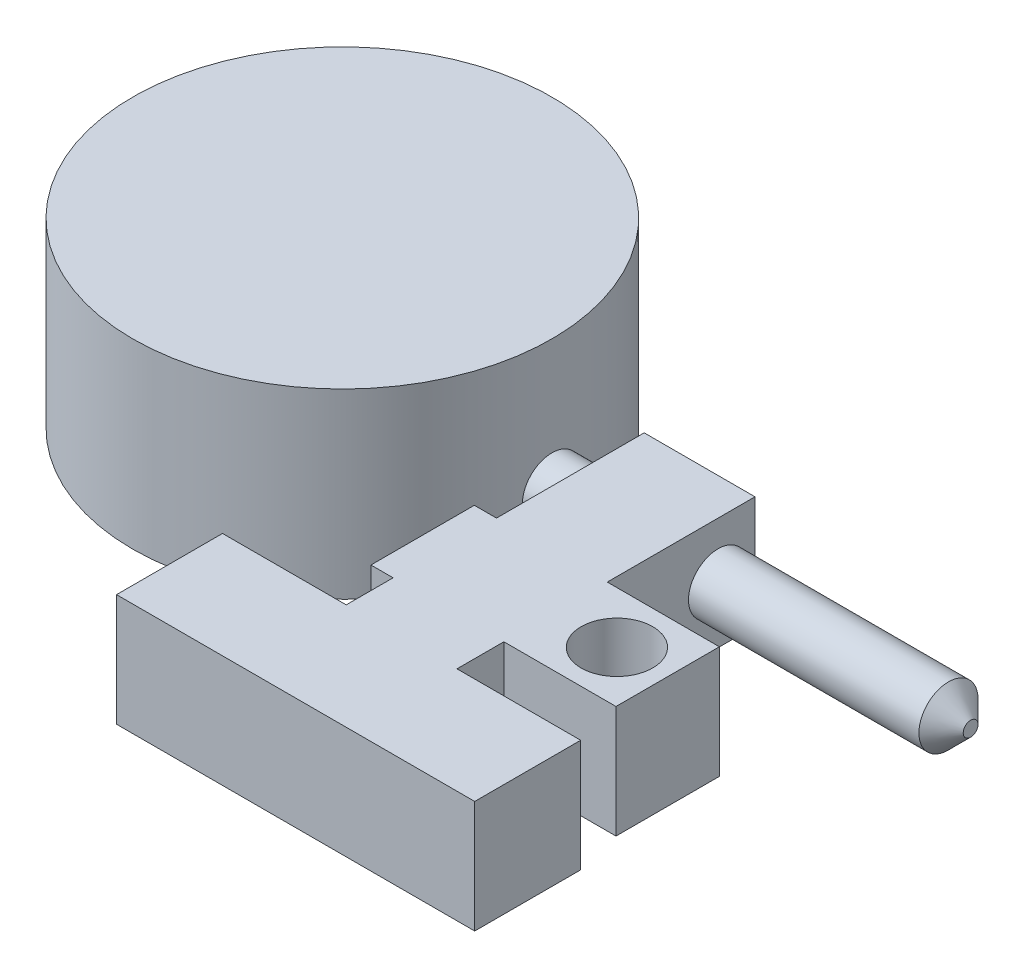
SolidWorks part; units mm, degrees
ref_plane "Front Plane" through (0, 0, 0) normal (0, 0, 1) x (1, 0, 0)
ref_plane "Top Plane" through (0, 0, 0) normal (0, 1, 0) x (1, 0, 0)
ref_plane "Right Plane" through (0, 0, 0) normal (1, 0, 0) x (0, 0, -1)
sketch "Sketch1" plane through (0, 0, 0) normal (0, 1, 0) x (1, 0, 0)
  circle A0 centre (0, 0) radius 28.375
  dimension "D1" = 56.75
extrude "Boss-Extrude1" add sketch "Sketch1" along normal blind 24.66
ref_plane "Plane1" through (28.375, 0, 0) normal (1, 0, 0) x (0, 0, -1)
sketch "Sketch3" plane through (28.375, 0, 0) normal (1, 0, 0) x (0, 0, -1)
  line L0 (0, 0) -> (0, 8.7554) construction
  line L1 (-28.375, 0) -> (28.375, 0) construction
  circle A0 centre (0, 7.3) radius 4
  dimension "D1" = 8
  dimension "D2" = 7.3
extrude "Boss-Extrude2" add sketch "Sketch3" along normal blind 56.7 separate body
chamfer "Chamfer1" distance 3 angle 45 1 edges at (85.075, 7.3, -4)
ref_plane "Plane2" through (0, 7.3, 0) normal (0, 1, 0) x (1, 0, 0)
sketch "Sketch5" plane through (0, 7.3, 0) normal (0, 1, 0) x (1, 0, 0)
  line L0 (35.875, 5) -> (35.875, -15)
  line L1 (35.875, -15) -> (32.875, -15)
  line L2 (32.875, -15) -> (32.875, -29)
  line L3 (32.875, -29) -> (35.875, -29)
  line L4 (35.875, -29) -> (35.875, -35.35)
  line L5 (35.875, -35.35) -> (19.125, -35.35)
  line L6 (19.125, -35.35) -> (19.125, -49.7)
  line L7 (19.125, -49.7) -> (67.625, -49.7)
  line L8 (67.625, -49.7) -> (67.625, -35.35)
  line L9 (67.625, -35.35) -> (50.875, -35.35)
  line L10 (50.875, -35.35) -> (50.875, -29)
  line L11 (50.875, -29) -> (66.055, -29)
  line L12 (66.055, -29) -> (66.055, -15)
  line L13 (66.055, -15) -> (50.875, -15)
  line L14 (50.875, -15) -> (50.875, 5)
  line L15 (50.875, 5) -> (35.875, 5)
  line L16 (28.375, -13.563) -> (28.375, 13.563) construction
  point P15 (43.375, 5)
  point P17 (43.375, -49.7)
  dimension "D1" = 15
  dimension "D2" = 15
  dimension "D3" = 14
  dimension "D4" = 5
  dimension "D5" = 20
  dimension "D6" = 6.35
  dimension "D7" = 48.5
  dimension "D8" = 14.35
  dimension "D9" = 15.18
  dimension "D10" = 3
extrude "Boss-Extrude3" add sketch "Sketch5" along normal mid plane 15.2
sketch "Sketch6" plane through (0, 14.9, 0) normal (0, 1, 0) x (1, 0, 0)
  line L0 (66.055, -22) -> (51.4493, -22) construction
  line L1 (66.055, -29) -> (66.055, -15) construction
  circle A0 centre (59.18, -22) radius 4.85
  point P4 (59.18, -22)
  dimension "D2" = 9.7
  dimension "D1" = 6.875
extrude "Cut-Extrude1" cut sketch "Sketch6" against normal up to next (15.2 mm away)
